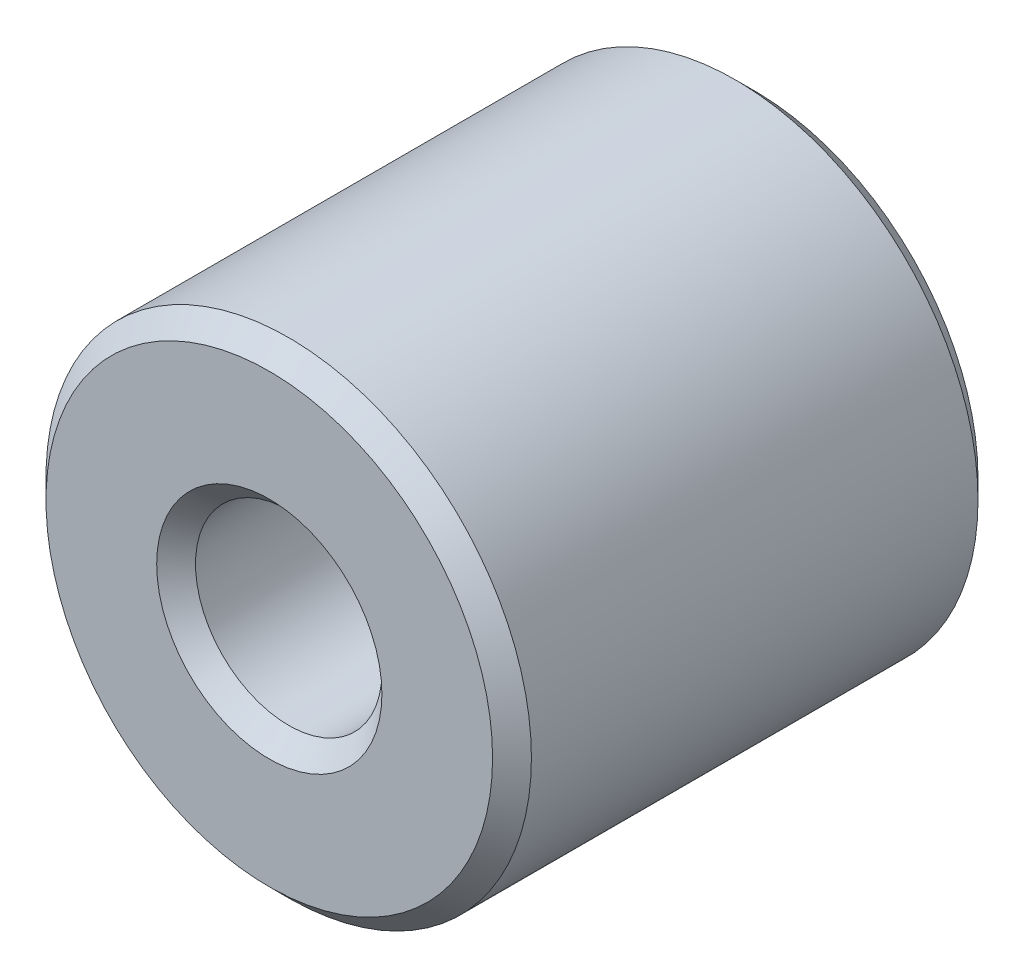
SolidWorks part; units mm, degrees
ref_plane "Front Plane" through (0, 0, 0) normal (0, 0, 1) x (1, 0, 0)
ref_plane "Top Plane" through (0, 0, 0) normal (0, 1, 0) x (1, 0, 0)
ref_plane "Right Plane" through (0, 0, 0) normal (1, 0, 0) x (0, 0, -1)
sketch "Sketch1" plane through (0, 0, 0) normal (0, 0, 1) x (1, 0, 0)
  circle A0 centre (0, 0) radius 6.35
  circle A1 centre (0, 0) radius 2.4384
  dimension "OD" = 12.7
  dimension "ID" = 4.8768
sketch "Sketch2" plane through (0, 0, 0) normal (1, 0, 0) x (0, 0, -1)
  line L0 (-6.35, 0) -> (6.35, 0) construction
  point P0 (6.35, 6.35)
  point P3 (0, 0)
  point P6 (-6.35, 6.35)
  point P7 (0, 6.35)
  dimension "Length" = 12.7
sketch "Sketch3" plane through (0, 0, 0) normal (0, 0, 1) x (1, 0, 0)
  circle A0 centre (0, 0) radius 6.35 construction
  circle A1 centre (0, 0) radius 2.4384 construction
  circle A2 centre (0, 0) radius 6.35
  circle A3 centre (0, 0) radius 2.4384
extrude "Boss-Extrude1" add sketch "Sketch3" against normal up to vertex (6.35 mm away) and the other way up to vertex (6.35 mm away) up to point (0, 0, -6.35) other way up to point (0, 0, 6.35)
chamfer "Chamfer1" distance 0.508 angle 45 4 edges at (6.35, 0, 6.35) (6.35, 0, -6.35) (2.4384, 0, -6.35) (2.4384, 0, 6.35)
sketch "Sketch4" plane through (0, 0, 0) normal (1, 0, 0) x (0, 0, -1)
  line L0 (5.842, 2.4384) -> (-5.842, 2.4384)
  line L1 (-5.842, -2.4384) -> (5.842, -2.4384)
  line L2 (-5.842, -2.4384) -> (5.842, -2.4384)
  line L3 (5.842, 2.4384) -> (-5.842, 2.4384)
equation "\"D1@Chamfer1\"=\"OD@Sketch1\"*.04"
